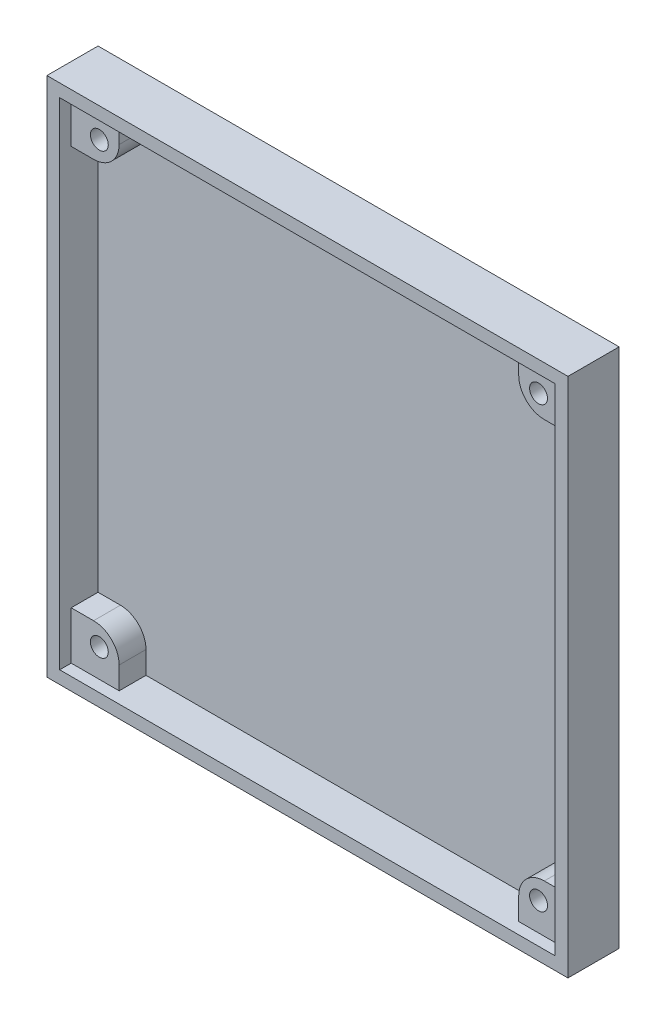
SolidWorks part; units mm, degrees
ref_plane "Front Plane" through (0, 0, 0) normal (0, 0, 1) x (1, 0, 0)
ref_plane "Top Plane" through (0, 0, 0) normal (0, 1, 0) x (1, 0, 0)
ref_plane "Right Plane" through (0, 0, 0) normal (1, 0, 0) x (0, 0, -1)
sketch "Sketch1" plane through (0, 0, 0) normal (0, 0, 1) x (1, 0, 0)
  line L1 (-38.75, 38.75) -> (38.75, 38.75) construction
  line L2 (-38.75, 38.75) -> (-38.75, -38.75) construction
  line L3 (-38.75, -38.75) -> (38.75, -38.75) construction
  line L4 (38.75, 38.75) -> (38.75, -38.75) construction
  line L5 (-38.75, 38.75) -> (38.75, -38.75) construction
  line L6 (-38.75, -38.75) -> (38.75, 38.75) construction
  line L7 (-40.75, 40.75) -> (40.75, 40.75)
  line L8 (-40.75, 40.75) -> (-40.75, -40.75)
  line L9 (-40.75, -40.75) -> (40.75, -40.75)
  line L10 (40.75, 40.75) -> (40.75, -40.75)
  line L11 (-40.75, 40.75) -> (40.75, -40.75) construction
  line L12 (-40.75, -40.75) -> (40.75, 40.75) construction
  point P0 (0, 0)
  point P6 (0, 0)
  dimension "D1" = 2
  dimension "D2" = 77.5
  dimension "D3" = 77.5
extrude "Boss-Extrude2" add sketch "Sketch1" along normal blind 8
sketch "Sketch3" plane through (0, 0, 8) normal (0, 0, 1) x (1, 0, 0)
  line L1 (-38.75, 38.75) -> (38.75, 38.75)
  line L2 (-38.75, 38.75) -> (-38.75, -38.75)
  line L3 (-38.75, -38.75) -> (38.75, -38.75)
  line L4 (38.75, 38.75) -> (38.75, -38.75)
  line L5 (-38.75, 38.75) -> (38.75, -38.75) construction
  line L6 (-38.75, -38.75) -> (38.75, 38.75) construction
  point P0 (0, 0)
extrude "Cut-Extrude2" cut sketch "Sketch3" against normal blind 6
sketch "Sketch5" plane through (0, 0, 2) normal (0, 0, 1) x (1, 0, 0)
  line L1 (-38.75, 38.75) -> (-31.25, 38.75)
  line L2 (-38.75, 38.75) -> (-38.75, 31.25)
  line L3 (-38.75, 31.25) -> (-31.25, 31.25)
  line L4 (-31.25, 38.75) -> (-31.25, 31.25)
  line L5 (38.75, 38.75) -> (31.25, 38.75)
  line L6 (38.75, 38.75) -> (38.75, 31.25)
  line L7 (38.75, 31.25) -> (31.25, 31.25)
  line L8 (31.25, 38.75) -> (31.25, 31.25)
  line L9 (38.75, -38.75) -> (31.25, -38.75)
  line L10 (38.75, -38.75) -> (38.75, -31.25)
  line L11 (38.75, -31.25) -> (31.25, -31.25)
  line L12 (31.25, -38.75) -> (31.25, -31.25)
  line L13 (-38.75, -38.75) -> (-31.25, -38.75)
  line L14 (-38.75, -38.75) -> (-38.75, -31.25)
  line L15 (-38.75, -31.25) -> (-31.25, -31.25)
  line L16 (-31.25, -38.75) -> (-31.25, -31.25)
  dimension "D1" = 7.5
extrude "Boss-Extrude3" add sketch "Sketch5" along normal blind 4.2
sketch "Sketch4" plane through (0, 0, 6.2) normal (0, 0, 1) x (1, 0, 0)
  line L0 (-34.35, 34.35) -> (34.35, 34.35) construction
  line L1 (34.35, 34.35) -> (34.35, -34.35) construction
  line L12 (34.35, -34.35) -> (-34.35, -34.35) construction
  line L13 (-34.35, -34.35) -> (-34.35, 34.35) construction
  line L14 (0, 38.75) -> (0, 34.35) construction
  line L15 (38.75, 38.75) -> (-38.75, 38.75) construction
  line L16 (34.35, 0) -> (38.75, 0) construction
  line L17 (38.75, -38.75) -> (38.75, 38.75) construction
  line L18 (0, -38.75) -> (0, -34.35) construction
  line L19 (-31.25, -38.75) -> (31.25, -38.75) construction
  line L20 (-38.75, 0) -> (-34.35, 0) construction
  line L21 (-38.75, 38.75) -> (-38.75, -38.75) construction
  circle A0 centre (-34.35, 34.35) radius 1.4
  circle A1 centre (34.35, 34.35) radius 1.4
  circle A2 centre (34.35, -34.35) radius 1.4
  circle A3 centre (-34.35, -34.35) radius 1.4
  dimension "D3" = 68.7
  dimension "D9" = 2.8
  dimension "D1" = 68.7
  dimension "D2" = 68.7
  dimension "D4" = 68.7
extrude "Cut-Extrude3" cut sketch "Sketch4" against normal blind 4.2
sketch "Sketch6" plane through (0, 0, 0) normal (0, 0, -1) x (-1, 0, 0)
  text T0 "<b>     XYZZY</b>\r\n<b>    MOTOR</b>\r\n<b>CONTROLLER</b>\r\n<b> PROTOTYPE</b>" font "Century Gothic" height in points 24
extrude "Cut-Extrude4" cut sketch "Sketch6" against normal blind 1
fillet "Fillet1" radius 4 4 edges at (31.25, -31.25, 4.1) (-31.25, -31.25, 4.1) (31.25, 31.25, 4.1) (-31.25, 31.25, 4.1)
sketch "Sketch7" plane through (0, 0, 0) normal (0, 0, -1) x (-1, 0, 0)
  line L0 (40.75, 40.75) -> (40.75, -40.75) construction
  line L1 (40.75, 0) -> (48.75, 0) construction
  line L2 (-40.75, -40.75) -> (-40.75, 40.75) construction
  line L5 (-40.75, -40.75) -> (-40.75, 40.75) construction
  line L6 (40.75, 8) -> (40.75, -8)
  line L7 (-40.75, -8) -> (-40.75, 8)
  line L10 (-48.75, 0) -> (-40.75, 0) construction
  arc A0 (40.75, 8) -> (40.75, -8) centre (40.75, 0) cw
  arc A1 (-40.75, 8) -> (-40.75, -8) centre (-40.75, 0) ccw
  circle A2 centre (44.75, 0) radius 2
  circle A3 centre (-44.75, 0) radius 2
  dimension "D3" = 4
  dimension "D1" = 8
extrude "Boss-Extrude4" [suppressed] add sketch "Sketch7" against normal blind 2
